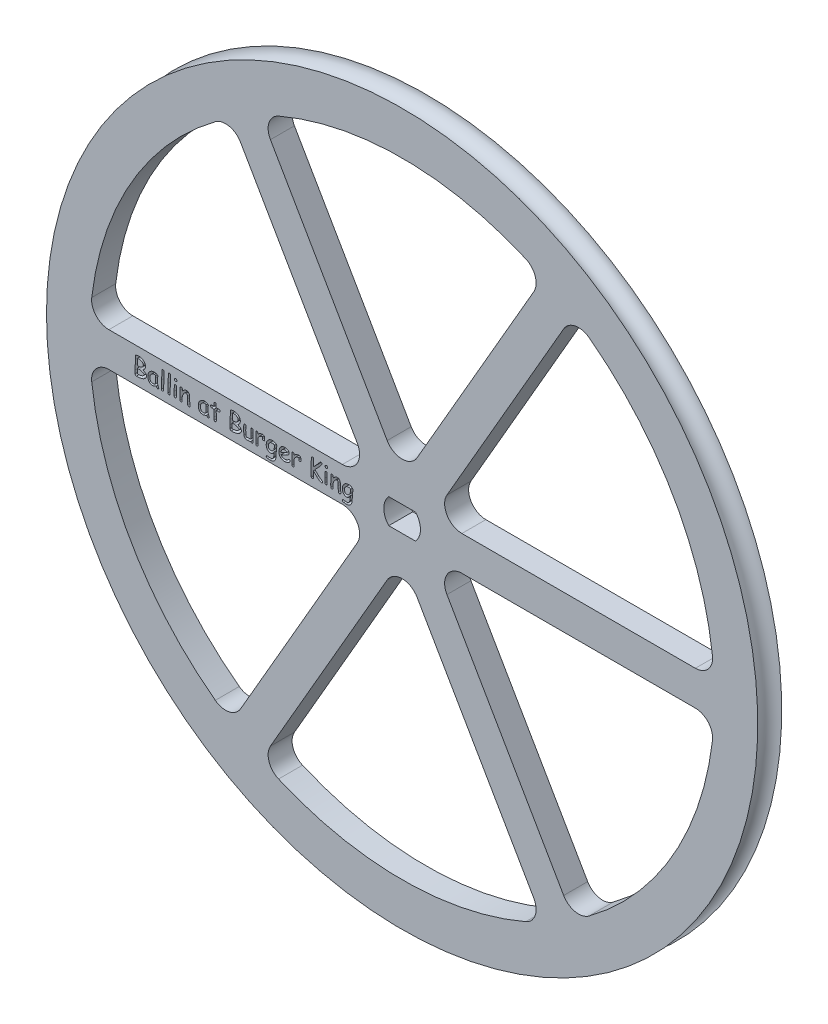
SolidWorks part; units mm, degrees
ref_plane "Front Plane" through (0, 0, 0) normal (0, 0, 1) x (1, 0, 0)
ref_plane "Top Plane" through (0, 0, 0) normal (0, 1, 0) x (1, 0, 0)
ref_plane "Right Plane" through (0, 0, 0) normal (1, 0, 0) x (0, 0, -1)
sketch "Sketch1" plane through (108.7888, 159.1207, 12.0043) normal (0, 1, 0) x (1, 0, 0)
  line L0 (-52.3621, -1.7653) -> (52.3621, -1.7653) construction
  line L1 (52.3621, 1.7653) -> (-52.3621, 1.7653) construction
  line L2 (-52.3621, -1.7653) -> (0, -1.7653)
  line L3 (0, 1.7653) -> (-52.3621, 1.7653)
  line L4 (0, 1.7653) -> (0, -1.7653)
  arc A0 (-52.3621, -1.7653) -> (-52.3621, 1.7653) centre (-52.3621, 0) ccw construction
  arc A1 (-52.3621, -1.7653) -> (-52.3621, 1.7653) centre (-52.3621, 0) ccw
  dimension "D1" = 52.3621
revolve "Revolve1" add sketch "Sketch1" angle 360 about L4
sketch "Sketch2" plane through (0, 0, 13.7696) normal (0, 0, 1) x (1, 0, 0)
  line L0 (56.4267, 159.1207) -> (108.7888, 159.1207) construction
  line L1 (108.7888, 159.1207) -> (82.6077, 204.4676) construction
  line L2 (85.0019, 195.2407) -> (102.1897, 165.4707)
  line L3 (99.9899, 161.6607) -> (65.6145, 161.6607)
  line L5 (106.5891, 168.0107) -> (89.4013, 197.7807)
  line L6 (69.1267, 160.3907) -> (102.4388, 160.3907) construction
  line L7 (69.1267, 160.3907) -> (69.1267, 157.8507) construction
  line L8 (69.1267, 157.8507) -> (102.4388, 157.8507) construction
  line L9 (102.4388, 160.3907) -> (102.4388, 157.8507) construction
  line L10 (128.1762, 197.7807) -> (110.9885, 168.0107)
  line L11 (115.3879, 165.4707) -> (132.5756, 195.2407)
  line L12 (151.963, 161.6607) -> (117.5876, 161.6607)
  line L13 (117.5876, 156.5807) -> (151.963, 156.5807)
  line L14 (132.5756, 123.0007) -> (115.3879, 152.7707)
  line L15 (110.9885, 150.2307) -> (128.1762, 120.4607)
  line L16 (89.4013, 120.4607) -> (106.5891, 150.2307)
  line L17 (102.1897, 152.7707) -> (85.0019, 123.0007)
  line L18 (65.6145, 156.5807) -> (99.9899, 156.5807)
  line L19 (106.8222, 157.2707) -> (110.7554, 157.2707)
  line L20 (110.7554, 160.9707) -> (106.8222, 160.9707)
  line L21 (106.0888, 159.1207) -> (111.4888, 159.1207) construction
  circle A0 centre (108.7888, 159.1207) radius 52.3621 construction
  arc A1 (81.2839, 196.0069) -> (63.0919, 164.4975) centre (108.7888, 159.1207) ccw
  arc A2 (102.1897, 165.4707) -> (99.9899, 161.6607) centre (99.9899, 164.2007) cw
  arc A3 (65.6145, 161.6607) -> (63.0919, 164.4975) centre (65.6145, 164.2007) cw
  arc A4 (85.0019, 195.2407) -> (81.2839, 196.0069) centre (82.8022, 193.9707) ccw
  arc A5 (126.9807, 201.3837) -> (90.5968, 201.3837) centre (108.7888, 159.1207) ccw
  arc A6 (128.1762, 197.7807) -> (126.9807, 201.3837) centre (125.9765, 199.0507) ccw
  arc A7 (89.4013, 197.7807) -> (90.5968, 201.3837) centre (91.601, 199.0507) cw
  arc A8 (110.9885, 168.0107) -> (106.5891, 168.0107) centre (108.7888, 169.2807) cw
  arc A9 (154.4856, 164.4975) -> (136.2937, 196.0069) centre (108.7888, 159.1207) ccw
  arc A10 (151.963, 161.6607) -> (154.4856, 164.4975) centre (151.963, 164.2007) ccw
  arc A11 (132.5756, 195.2407) -> (136.2937, 196.0069) centre (134.7753, 193.9707) cw
  arc A12 (117.5876, 161.6607) -> (115.3879, 165.4707) centre (117.5876, 164.2007) cw
  arc A13 (136.2937, 122.2344) -> (154.4856, 153.7439) centre (108.7888, 159.1207) ccw
  arc A14 (132.5756, 123.0007) -> (136.2937, 122.2344) centre (134.7753, 124.2707) ccw
  arc A15 (151.963, 156.5807) -> (154.4856, 153.7439) centre (151.963, 154.0407) cw
  arc A16 (115.3879, 152.7707) -> (117.5876, 156.5807) centre (117.5876, 154.0407) cw
  arc A17 (90.5968, 116.8576) -> (126.9807, 116.8576) centre (108.7888, 159.1207) ccw
  arc A18 (89.4013, 120.4607) -> (90.5968, 116.8576) centre (91.601, 119.1907) ccw
  arc A19 (128.1762, 120.4607) -> (126.9807, 116.8576) centre (125.9765, 119.1907) cw
  arc A20 (106.5891, 150.2307) -> (110.9885, 150.2307) centre (108.7888, 148.9607) cw
  arc A21 (63.0919, 153.7439) -> (81.2839, 122.2344) centre (108.7888, 159.1207) ccw
  arc A22 (65.6145, 156.5807) -> (63.0919, 153.7439) centre (65.6145, 154.0407) ccw
  arc A23 (85.0019, 123.0007) -> (81.2839, 122.2344) centre (82.8022, 124.2707) cw
  arc A24 (99.9899, 156.5807) -> (102.1897, 152.7707) centre (99.9899, 154.0407) cw
  arc A26 (110.7554, 157.2707) -> (110.7554, 160.9707) centre (108.7888, 159.1207) ccw
  arc A27 (106.8222, 160.9707) -> (106.8222, 157.2707) centre (108.7888, 159.1207) ccw
  text T0 "Ballin at Burger King" font "Comic Sans MS" height 2.54
  point P20 (69.1267, 159.1207)
  point P24 (108.7888, 159.1207)
  point P70 (108.7888, 159.1207)
  dimension "D4" = 6.35
  dimension "D5" = 2.54
  dimension "D1" = 60
  dimension "D2" = 2.54
  dimension "D3" = 2.54
  dimension "D6" = 12.7
  dimension "D7" = 6.35
  dimension "D8" = 2.54
  dimension "D9" = 6
  dimension "D10" = 3.9332
  dimension "D11" = 3.7
  dimension "D14" = 5.4
extrude "Cut-Extrude1" cut sketch "Sketch2" against normal up to surface (3.5306 mm away) up to face at (56.4267, 159.1207, 10.239)
ref_plane "Plane1" through (0, 0, 12.0043) normal (0, 0, 1) x (1, 0, 0)
ref_plane "Plane2" through (0, 159.1207, 0) normal (0, -1, 0) x (-1, 0, 0)
ref_plane "Plane3" through (108.7888, 0, 0) normal (1, 0, 0) x (0, 0, -1)
